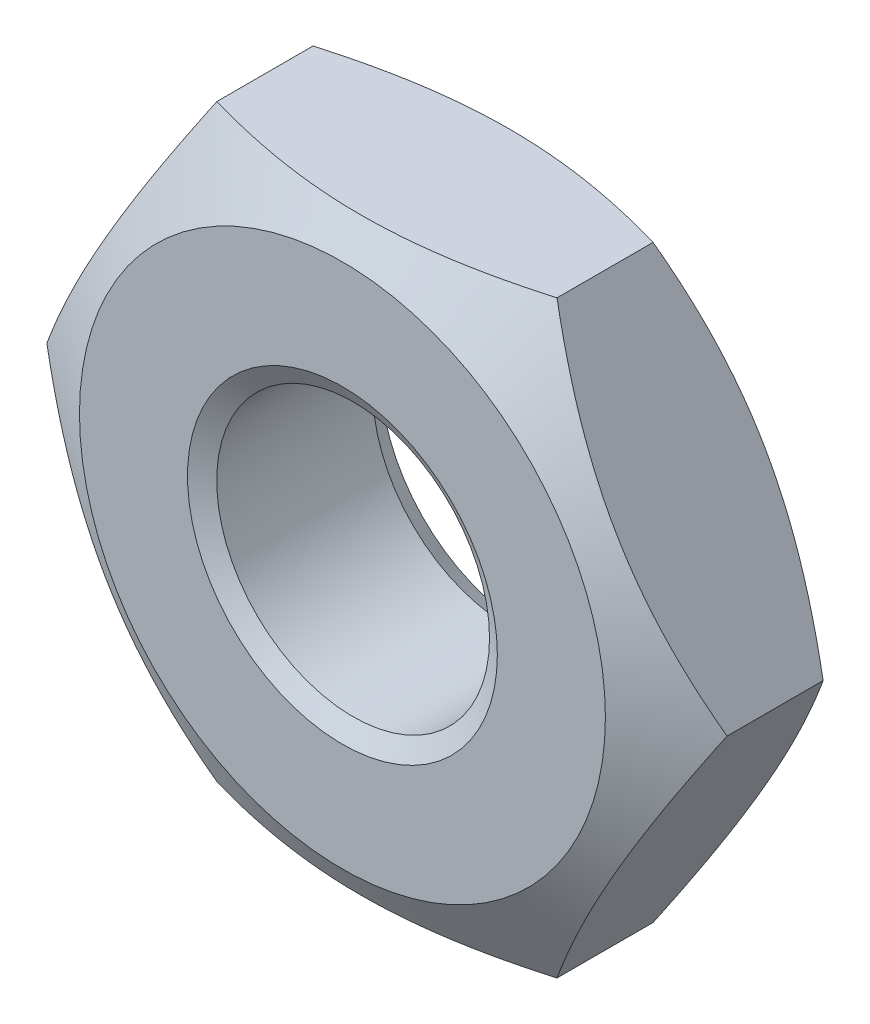
SolidWorks part; units mm, degrees
ref_plane "Front" through (0, 0, 0) normal (0, 0, 1) x (1, 0, 0)
ref_plane "Top" through (0, 0, 0) normal (0, 1, 0) x (1, 0, 0)
ref_plane "Right" through (0, 0, 0) normal (1, 0, 0) x (0, 0, -1)
sketch "Sketch1" plane through (0, 0, 0) normal (0, 0, 1) x (1, 0, 0)
  line L1 (2.0207, -3.5) -> (4.0415, 0)
  line L2 (4.0415, 0) -> (2.0207, 3.5)
  line L3 (2.0207, 3.5) -> (-2.0207, 3.5)
  line L4 (-2.0207, 3.5) -> (-4.0415, 0)
  line L5 (-4.0415, 0) -> (-2.0207, -3.5)
  line L6 (-2.0207, -3.5) -> (2.0207, -3.5)
  circle A0 centre (0, 0) radius 3.5 construction
  circle A1 centre (0, 0) radius 1.621
  dimension "D" = 3.242
  dimension "s" = 7
extrude "BaseNut" add sketch "Sketch1" against normal blind 2.2
cosmetic thread "ThreadCosmetic1" parameters "D"=4
sketch "Sketch2" plane through (0, 0, 0) normal (0, 1, 0) x (1, 0, 0)
  line L0 (-4.0415, 2.2) -> (-3.125, 2.2)
  line L2 (-3.125, 2.2) -> (-4.0415, 1.6709)
  line L3 (-4.0415, 1.6709) -> (-4.0415, 2.2)
  line L4 (0, 3.3759) -> (0, -9.8171) construction
  line L6 (-9.7712, 1.1) -> (9.8853, 1.1) construction
  line L7 (-4.0415, 0.5291) -> (-4.0415, 0)
  line L8 (-3.125, 0) -> (-4.0415, 0.5291)
  line L9 (-4.0415, 0) -> (-3.125, 0)
  dimension "D1" = 30
  dimension "dw" = 6.25
  dimension "D2" = 1.1
revolve "Double-Chamfer" cut sketch "Sketch2" angle 360 about L4
chamfer "EndChamfer" distance 0.22 angle 30 2 edges at (1.621, 0, -2.2) (1.621, 0, 0)
sketch "Sketch3" plane through (0, 0, 0) normal (0, 1, 0) x (1, 0, 0)
  line L0 (0, 6.7075) -> (0, -2.1252) construction
  line L1 (1.242, 2.1695) -> (1.621, 2.1695)
  line L2 (1.621, 2.1695) -> (1.9492, 1.98)
  line L3 (1.9492, 1.98) -> (1.621, 1.7905)
  line L4 (1.621, 1.7905) -> (1.242, 1.7905)
  line L5 (1.242, 1.7905) -> (1.242, 2.1695)
  line L6 (1.621, 1.98) -> (-1.621, 1.98) construction
  dimension "D1" = 0.379
  dimension "D2" = 3.242
revolve "Cut-Revolve10" [suppressed] cut sketch "Sketch3" angle 360 about L0
pattern_linear "LPattern10" [suppressed] count 4 spacing 0.4548 along (0, 0, 1)
equation "\"dw@Sketch2\" = \"s@Sketch1\"-0.75"
equation "\"D2@Sketch2\" = \"m@BaseNut\" / 2"
equation "\"D1@EndChamfer\" = \"m@BaseNut\" / 10"
equation "\"D2@Sketch3\" = \"D@Sketch1\""
equation "\"D1@Sketch3\" = (  \"D@ThreadCosmetic1\" - \"D@Sketch1\" )  / 2"
equation "\"D3@LPattern10\" = \"D1@Sketch3\" * 1.2"
equation "\"D1@LPattern10\" = (  \"m@BaseNut\" - \"D1@EndChamfer\" )  / \"D3@LPattern10\" "
